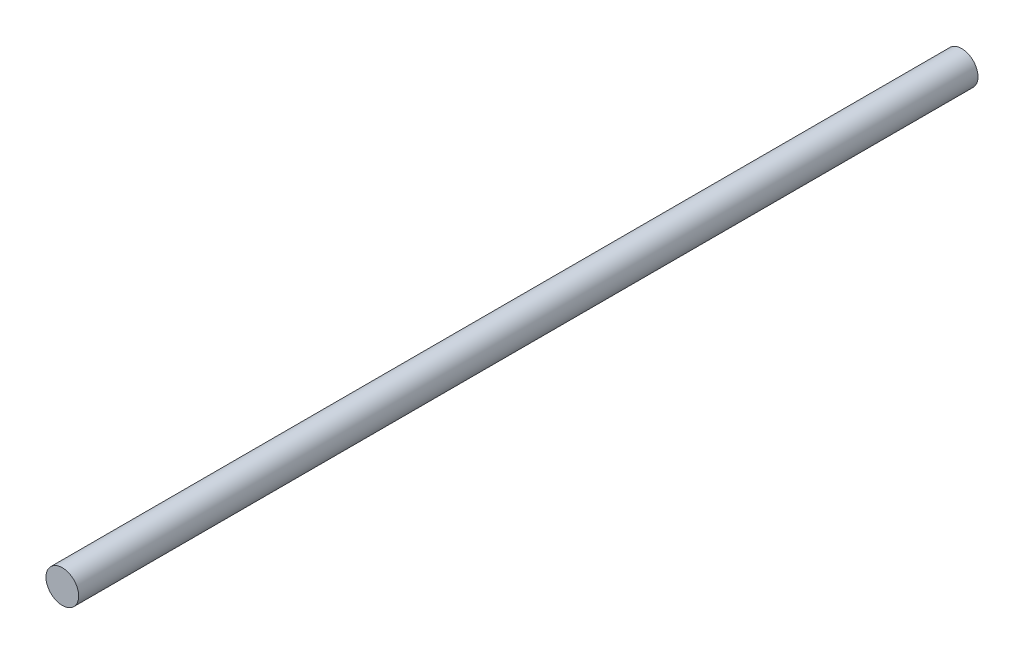
SolidWorks part; units mm, degrees
material "AISI 304"
ref_plane "Front Plane" through (0, 0, 0) normal (0, 0, 1) x (1, 0, 0)
ref_plane "Top Plane" through (0, 0, 0) normal (0, 1, 0) x (1, 0, 0)
ref_plane "Right Plane" through (0, 0, 0) normal (1, 0, 0) x (0, 0, -1)
sketch "Sketch1" plane through (0, 0, 0) normal (0, 0, 1) x (1, 0, 0)
  circle A0 centre (0, 0) radius 3
  dimension "D1" = 6
extrude "Boss-Extrude1" add sketch "Sketch1" along normal blind 165
